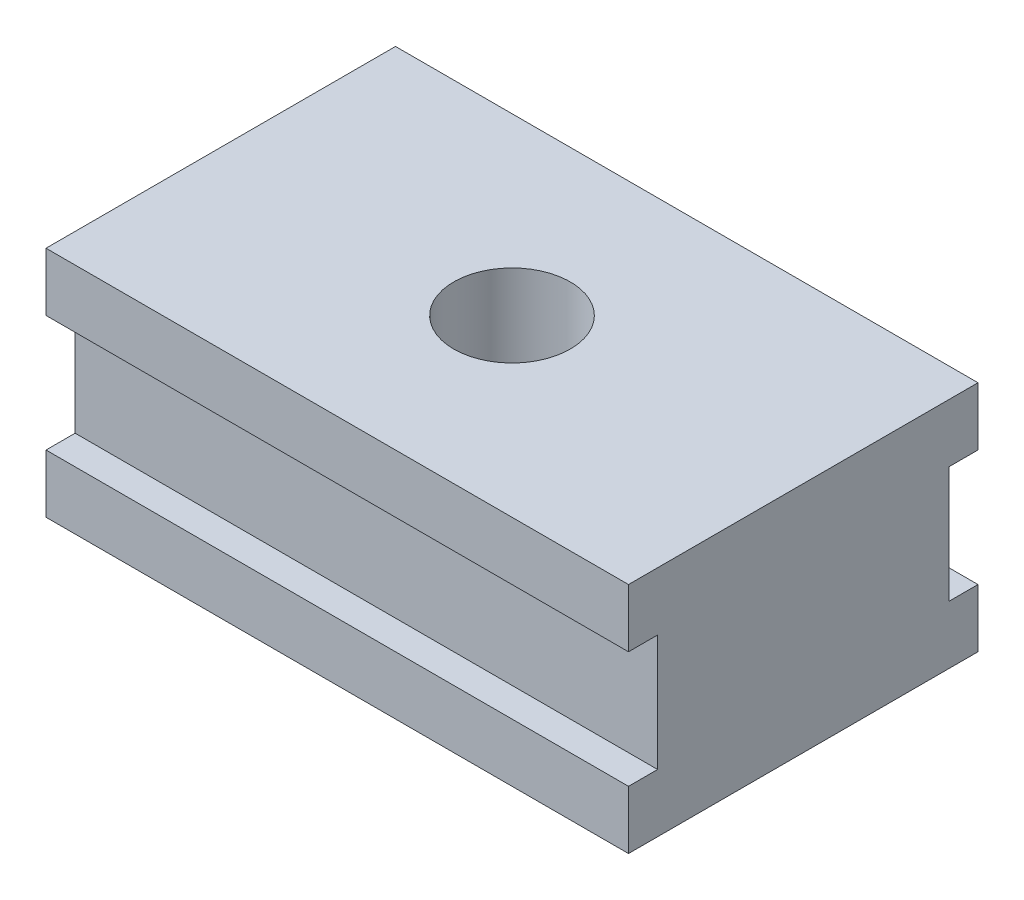
SolidWorks part; units mm, degrees
ref_plane "前视基准面" through (0, 0, 0) normal (0, 0, 1) x (1, 0, 0)
ref_plane "上视基准面" through (0, 0, 0) normal (0, 1, 0) x (1, 0, 0)
ref_plane "右视基准面" through (0, 0, 0) normal (1, 0, 0) x (0, 0, -1)
sketch "草图1" plane through (0, 0, 0) normal (0, 0, 1) x (1, 0, 0)
  line L1 (-10, 4) -> (10, 4)
  line L2 (-10, 4) -> (-10, -4)
  line L3 (-10, -4) -> (10, -4)
  line L4 (10, 4) -> (10, -4)
  line L5 (-10, 4) -> (10, -4) construction
  line L6 (-10, -4) -> (10, 4) construction
  point P0 (0, 0)
  dimension "D1" = 8
  dimension "D2" = 20
extrude "凸台-拉伸1" add sketch "草图1" along normal blind 12
sketch "草图2" plane through (10, 0, 0) normal (1, 0, 0) x (0, 0, -1)
  line L0 (-12, -4) -> (-12, 4) construction
  line L3 (0, 2) -> (-1, 2)
  line L4 (0, -2) -> (-1, -2)
  line L5 (-12, 2) -> (-11, 2)
  line L6 (-1, 2) -> (-1, -2)
  line L7 (0, 2) -> (0, -2)
  line L8 (-12, 2) -> (-12, -2)
  line L9 (-12, -2) -> (-11, -2)
  line L10 (-11, 2) -> (-11, -2)
  dimension "D4" = 1
  dimension "D1" = 1
sketch "草图3" plane through (0, 4, 0) normal (0, 1, 0) x (1, 0, 0)
  line L0 (0, 0) -> (0, -12)
  line L1 (10, 0) -> (-10, 0) construction
  line L2 (10, -12) -> (-10, -12) construction
  circle A0 centre (0, -6) radius 2
extrude "切除-拉伸3" cut sketch "草图2" against normal through all
extrude "切除-拉伸4" cut sketch "草图3" against normal through all contours L0 A0 | L0 A0
